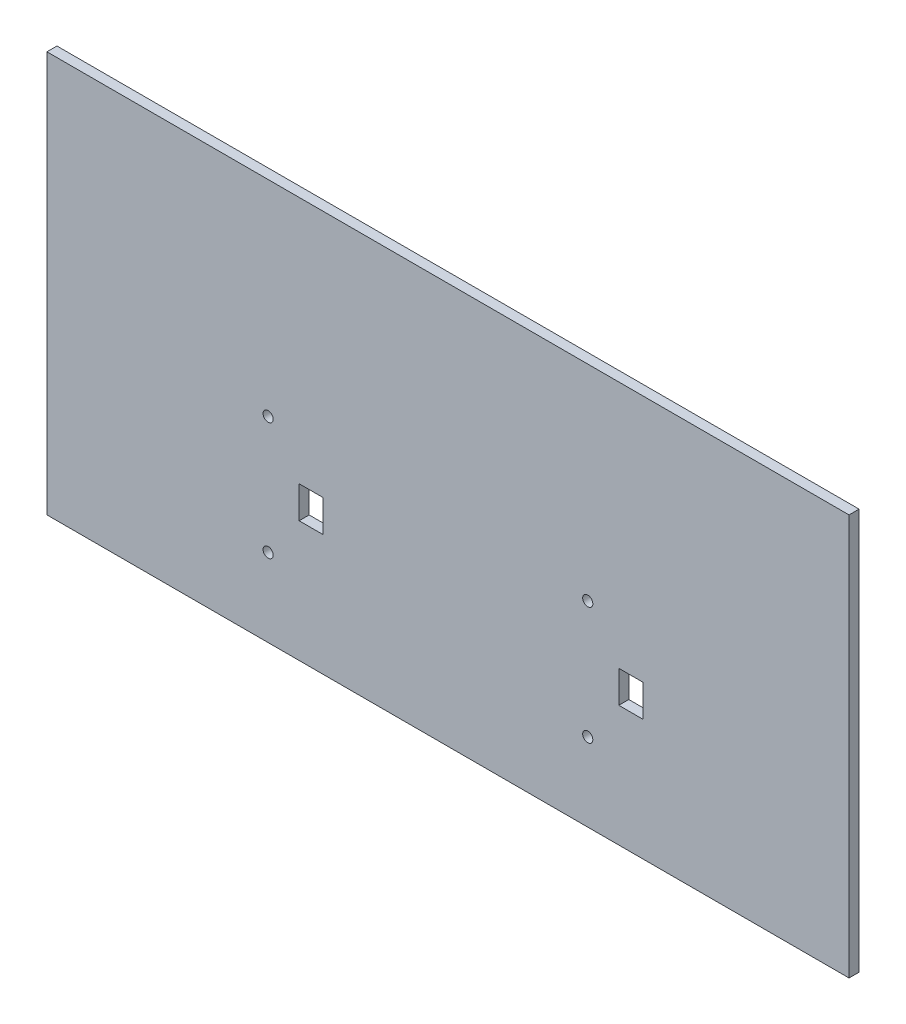
SolidWorks part; units mm, degrees
ref_plane "Front Plane" through (0, 0, 0) normal (0, 0, 1) x (1, 0, 0)
ref_plane "Top Plane" through (0, 0, 0) normal (0, 1, 0) x (1, 0, 0)
ref_plane "Right Plane" through (0, 0, 0) normal (1, 0, 0) x (0, 0, -1)
sketch "Sketch1" plane through (0, 0, 0) normal (0, 0, 1) x (1, 0, 0)
  line L1 (-127, -63.5) -> (127, -63.5)
  line L2 (-127, -63.5) -> (-127, 63.5)
  line L3 (-127, 63.5) -> (127, 63.5)
  line L4 (127, -63.5) -> (127, 63.5)
  line L5 (-127, -63.5) -> (127, 63.5) construction
  line L6 (-127, 63.5) -> (127, -63.5) construction
  point P0 (0, 0)
  dimension "D1" = 254
  dimension "D2" = 127
extrude "Boss-Extrude1" add sketch "Sketch1" along normal mid plane 3.175
sketch "Sketch2" plane through (0, 0, 1.5875) normal (0, 0, 1) x (1, 0, 0)
  line L0 (-47.13, -25.175) -> (-47.13, -15.025)
  line L1 (-47.13, -25.175) -> (-39.51, -25.175)
  line L2 (-47.13, -15.025) -> (-39.51, -15.025)
  line L3 (-39.51, -25.175) -> (-39.51, -15.025)
  line L4 (54.08, -15.025) -> (54.08, -25.175)
  line L5 (54.08, -15.025) -> (61.7, -15.025)
  line L6 (54.08, -25.175) -> (61.7, -25.175)
  line L7 (61.7, -15.025) -> (61.7, -25.175)
  circle A0 centre (-56.955, -1.46) radius 1.61
  circle A1 centre (-56.955, -38.74) radius 1.61
  circle A2 centre (44.255, -38.74) radius 1.61
  circle A3 centre (44.255, -1.46) radius 1.61
  dimension "D2" = 3.22
  dimension "D3" = 7.62
  dimension "D1" = 7.62
extrude "Cut-Extrude1" cut sketch "Sketch2" against normal blind 5.08
